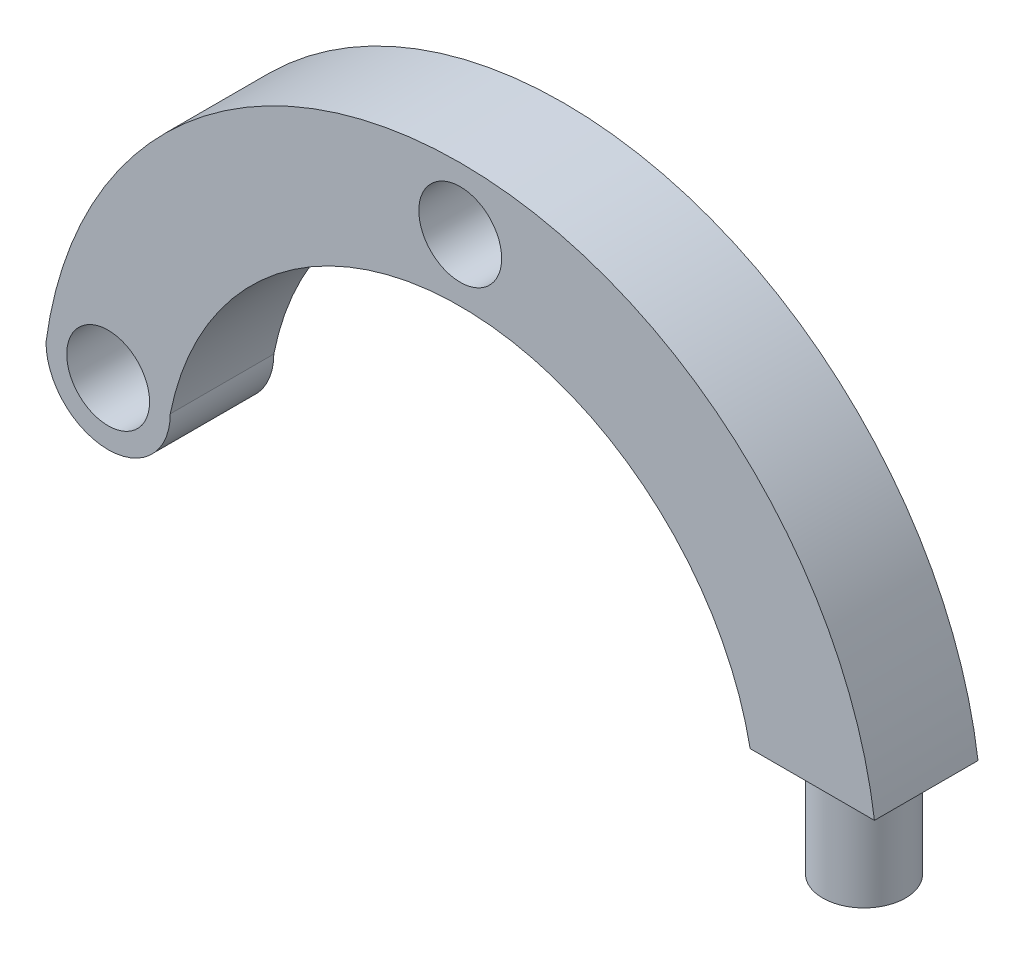
SolidWorks part; units mm, degrees
ref_plane "Alzado" through (0, 0, 0) normal (0, 0, 1) x (1, 0, 0)
ref_plane "Planta" through (0, 0, 0) normal (0, 1, 0) x (1, 0, 0)
ref_plane "Vista lateral" through (0, 0, 0) normal (1, 0, 0) x (0, 0, -1)
sketch "Croquis1" plane through (0, 0, 0) normal (0, 0, 1) x (1, 0, 0)
  line L0 (0, 20) -> (0, 30) construction
  line L1 (0, -20) -> (0, -145) construction
  line L2 (0, -145) -> (-200, -145) construction
  line L3 (0, -145) -> (200, -145) construction
  line L4 (0, 30) -> (50.1134, 30) construction
  line L5 (50.1134, 30) -> (50.1134, -30) construction
  line L6 (50.1134, -30) -> (0, -30) construction
  line L7 (-200, -145) -> (-200, -69.2255) construction
  line L8 (-200, -69.2255) -> (-140, -69.2255) construction
  line L9 (-140, -69.2255) -> (-140, -145) construction
  line L10 (140, -69.2255) -> (140, -145) construction
  line L11 (140, -145) -> (200, -145)
  circle A0 centre (0, 0) radius 20
  arc A1 (200, -145) -> (-200, -145) centre (0, -171.7857) ccw
  arc A2 (140, -145) -> (-140, -145) centre (0, -172.7174) ccw
  arc A3 (-200, -145) -> (-140, -145) centre (-170, -145) ccw
  circle A4 centre (-170, -145) radius 20
  dimension "D1" = 40
  dimension "D7" = 40
  dimension "D2" = 10
  dimension "D3" = 125
  dimension "D4" = 200
  dimension "D5" = 60
  dimension "D6" = 60
extrude "Saliente-Extruir1" add sketch "Croquis1" along normal blind 50
sketch "Croquis2" plane through (0, -145, 0) normal (0, -1, 0) x (1, 0, 0)
  line L0 (170, 50) -> (170, 0) construction
  line L1 (140, 50) -> (200, 50) construction
  circle A0 centre (170, 25) radius 20
  point P8 (0, 0)
  point P9 (0, 0)
  dimension "D1" = 40
extrude "Saliente-Extruir2" add sketch "Croquis2" along normal blind 50
